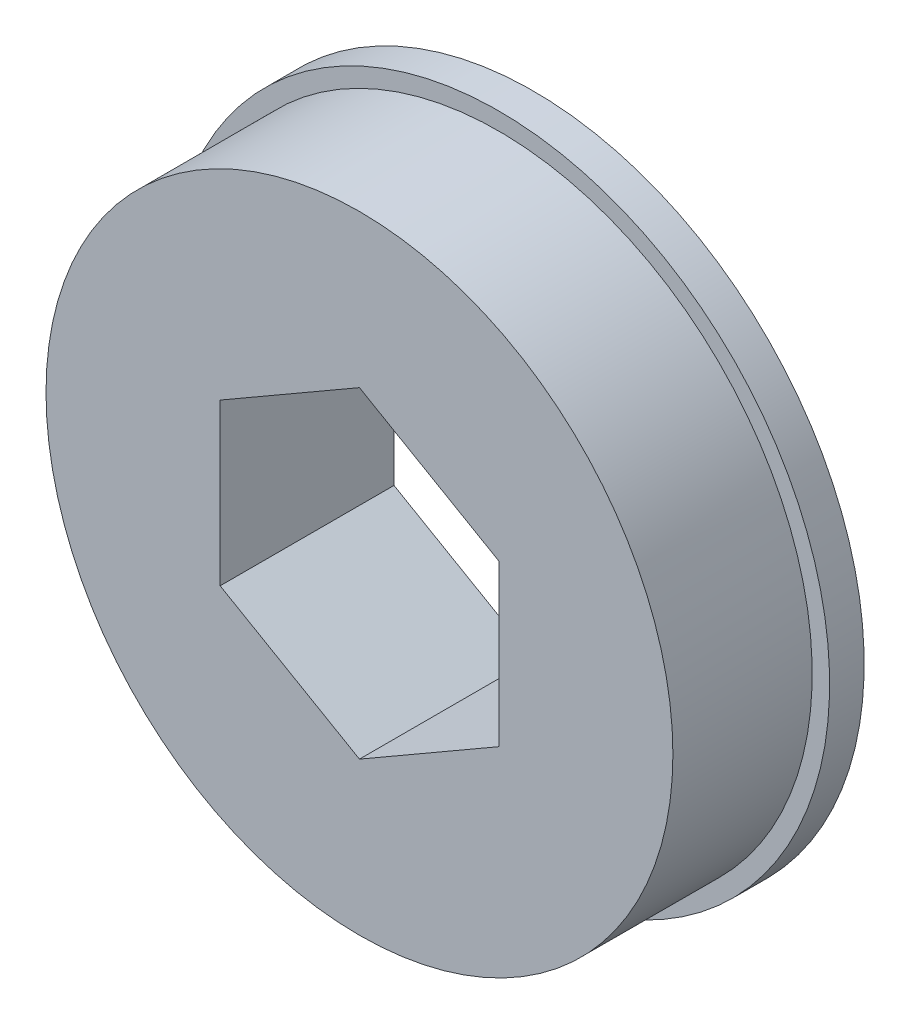
SolidWorks part; units mm, degrees
ref_plane "Front Plane" through (0, 0, 0) normal (0, 0, 1) x (1, 0, 0)
ref_plane "Top Plane" through (0, 0, 0) normal (0, 1, 0) x (1, 0, 0)
ref_plane "Right Plane" through (0, 0, 0) normal (1, 0, 0) x (0, 0, -1)
sketch "Sketch1" plane through (0, 0, 0) normal (0, 0, 1) x (1, 0, 0)
  line L0 (0, 7.3323) -> (0, 0) construction
  line L1 (6.35, 3.6662) -> (0, 7.3323)
  line L2 (0, 7.3323) -> (-6.35, 3.6662)
  line L3 (-6.35, 3.6662) -> (-6.35, -3.6662)
  line L4 (-6.35, -3.6662) -> (0, -7.3323)
  line L5 (0, -7.3323) -> (6.35, -3.6662)
  line L6 (6.35, -3.6662) -> (6.35, 3.6662)
  circle A0 centre (0, 0) radius 14.2875
  circle A1 centre (0, 0) radius 6.35 construction
  dimension "D1" = 28.575
  dimension "D2" = 12.7
extrude "Boss-Extrude1" add sketch "Sketch1" along normal blind 6.35
sketch "Sketch2" plane through (0, 0, 0) normal (0, 0, -1) x (-1, 0, 0)
  line L0 (0, 0) -> (0, 7.3323) construction
  line L1 (0, 7.3323) -> (-6.35, 3.6662)
  line L2 (-6.35, 3.6662) -> (-6.35, -3.6662)
  line L3 (-6.35, -3.6662) -> (0, -7.3323)
  line L4 (0, -7.3323) -> (6.35, -3.6662)
  line L5 (6.35, -3.6662) -> (6.35, 3.6662)
  line L6 (6.35, 3.6662) -> (0, 7.3323)
  circle A0 centre (0, 0) radius 15.0813
  circle A1 centre (0, 0) radius 6.35 construction
  dimension "D1" = 30.1625
  dimension "D2" = 12.7
extrude "Boss-Extrude2" add sketch "Sketch2" along normal blind 1.5748
